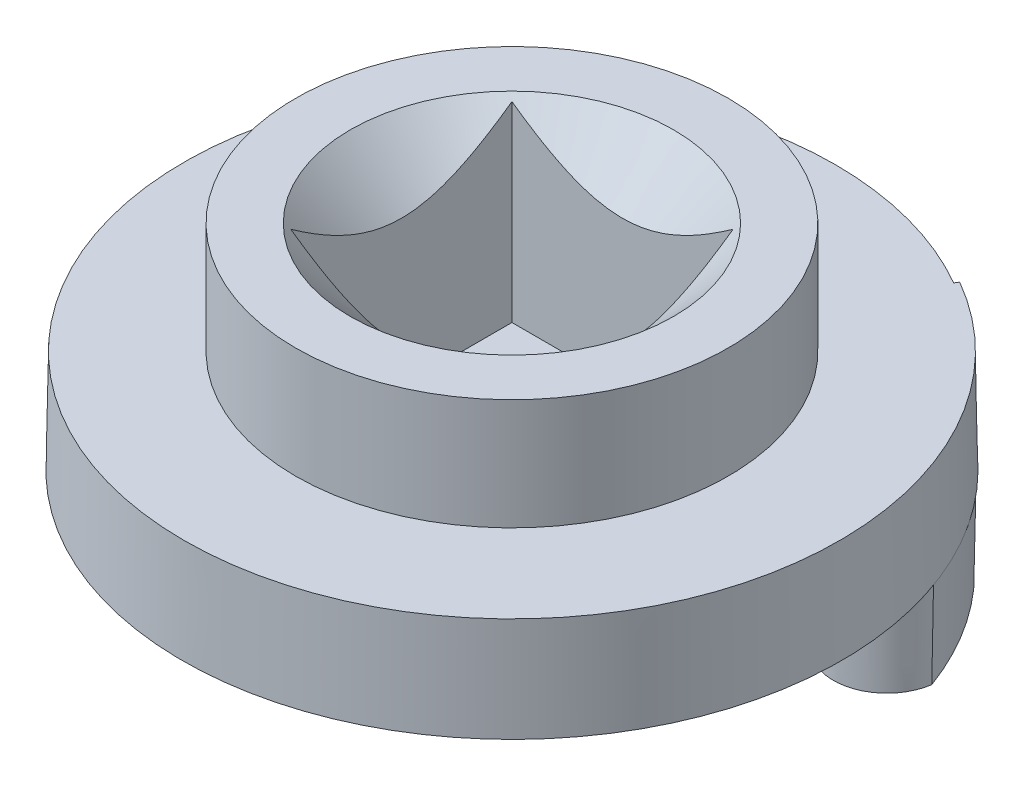
SolidWorks part; units mm, degrees
ref_plane "Front" through (0, 0, 0) normal (0, 0, 1) x (1, 0, 0)
ref_plane "Top" through (0, 0, 0) normal (0, 1, 0) x (1, 0, 0)
ref_plane "Right" through (0, 0, 0) normal (1, 0, 0) x (0, 0, -1)
sketch "Sketch1" plane through (0, 0, 0) normal (0, 0, 1) x (1, 0, 0)
  line L0 (0, -4.1211) -> (0, 10.7712) construction
  line L1 (0, 0) -> (9.525, 0)
  line L2 (9.525, 0) -> (9.525, 2.9972)
  line L3 (9.525, 2.9972) -> (6.2865, 2.9972)
  line L4 (6.2865, 2.9972) -> (6.2865, 6.223)
  line L5 (6.2865, 6.223) -> (0, 6.223)
  line L6 (0, 6.223) -> (0, 0)
  dimension "D1" = 2.9972
  dimension "D2" = 6.223
  dimension "D3" = 6.2865
  dimension "D4" = 9.525
revolve "Revolve1" add sketch "Sketch1" angle 360 about L0
ref_plane "Plane2" through (0, 0.508, 0) normal (0, 1, 0) x (1, 0, 0)
sketch "Sketch2" plane through (0, 0.508, 0) normal (0, 1, 0) x (1, 0, 0)
  line L0 (2.9555, 0) -> (0, 0) construction
  line L1 (0, 0) -> (0, 2.7196) construction
  line L3 (-3.2131, 3.2131) -> (3.2131, 3.2131)
  line L4 (-3.2131, 3.2131) -> (-3.2131, -3.2131)
  line L5 (-3.2131, -3.2131) -> (3.2131, -3.2131)
  line L6 (3.2131, 3.2131) -> (3.2131, -3.2131)
  dimension "D1" = 6.4262
  dimension "D2" = 6.4262
sketch "Sketch3" plane through (0, 0, 0) normal (0, 0, 1) x (1, 0, 0)
  line L0 (0, 0) -> (0, 12.681) construction
  line L1 (-9.525, 0) -> (9.525, 0) construction
  line L2 (0, 6.223) -> (4.699, 6.223)
  line L3 (6.2865, 6.223) -> (-6.2865, 6.223) construction
  line L4 (4.699, 6.223) -> (0, 1.524)
  line L5 (0, 1.524) -> (0, 6.223)
  dimension "D1" = 4.699
  dimension "D2" = 45
extrude "Cut-Extrude1" cut sketch "Sketch2" along normal through all
revolve "Cut-Revolve1" cut sketch "Sketch3" angle 360 about L0
draft "Draft1" type of draft neutral plane draft angle 1 faces to draft 1 face at (0, 2.9972, -9.525) neutral plane through (9.525, 2.9972, 0) neutral plane normal (0, 1, 0) parameters "D1"=1
sketch "Sketch4" plane through (0, 0, 0) normal (0, -1, 0) x (1, 0, 0)
  arc A0 (5.3378, -3.856) -> (7.181, -6.3027) centre (6.6294, -4.8006) ccw
  arc A1 (9.0005, -3.2507) -> (5.9716, -2.7928) centre (7.4168, -3.4798) ccw
  arc A2 (5.3378, -3.856) -> (5.9716, -2.7928) centre (0.0071, 0.0424) ccw
  arc A3 (7.181, -6.3027) -> (9.0005, -3.2507) centre (0.0071, 0.0424) ccw
  circle A4 centre (0, 0) radius 9.5773 construction
  point P0 (6.6294, -4.8006)
  point P1 (7.4168, -3.4798)
  dimension "D5" = 3.2004
  dimension "D6" = 6.604
  dimension "D1" = 6.6294
  dimension "D2" = 4.8006
  dimension "D3" = 7.4168
  dimension "D4" = 3.4798
extrude "Boss-Extrude2" add sketch "Sketch4" along normal blind 2.54 draft 1
sketch "Sketch5" plane through (0, 0, 0) normal (0, -1, 0) x (1, 0, 0)
  line L0 (0, 0) -> (-7.5772, 6.5868) construction
  line L1 (0, 0) -> (0, 7.021) construction
  line L2 (0, 0) -> (-7.3124, 0) construction
  line L3 (-6.1593, 5.6908) -> (-7.0589, 6.4728)
  line L5 (-7.3922, 6.0894) -> (-6.4926, 5.3074)
  line L6 (-6.4926, 5.3074) -> (-6.1593, 5.6908)
  arc A0 (-7.0589, 6.4728) -> (-7.3922, 6.0894) centre (0, 0) ccw
  circle A2 centre (0, 0) radius 9.5773 construction
  dimension "D1" = 41
  dimension "D2" = 8.382
  dimension "D3" = 0.508
extrude "Boss-Extrude3" add sketch "Sketch5" along normal blind 0.508 draft 1
sketch "Sketch6" plane through (0, 2.9972, 0) normal (0, 1, 0) x (1, 0, 0)
  line L0 (0, 0) -> (-5.6838, 9.8446) construction
  line L1 (-5.08, 8.7988) -> (-4.699, 8.1389)
  line L2 (0, 10.0311) -> (0, 0) construction
  line L3 (0, 0) -> (5.5716, 9.6503) construction
  line L4 (4.699, 8.1389) -> (5.08, 8.7988)
  arc A0 (4.699, 8.1389) -> (-4.699, 8.1389) centre (0, 0) ccw
  arc A1 (5.08, 8.7988) -> (-5.08, 8.7988) centre (0, 0) ccw
  dimension "D3" = 9.398
  dimension "D4" = 10.16
  dimension "D1" = 30
  dimension "D2" = 30
extrude "Cut-Extrude2" cut sketch "Sketch6" against normal through all draft 1
